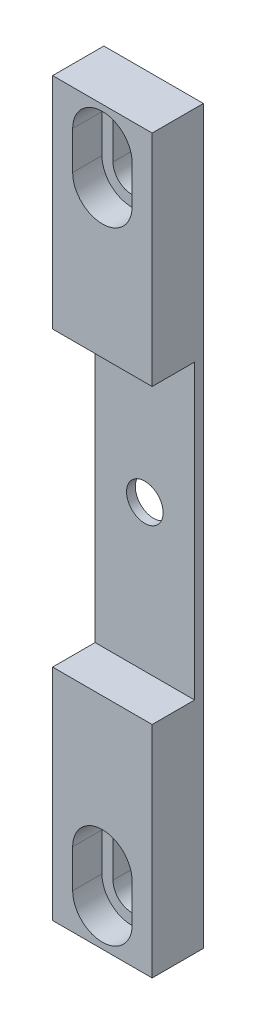
SolidWorks part; units mm, degrees
material "6061-T6 Al"
ref_plane "Front Plane" through (0, 0, 0) normal (0, 0, 1) x (1, 0, 0)
ref_plane "Top Plane" through (0, 0, 0) normal (0, 1, 0) x (1, 0, 0)
ref_plane "Right Plane" through (0, 0, 0) normal (1, 0, 0) x (0, 0, -1)
sketch "Sketch1" plane through (0, 0, 0) normal (0, 0, 1) x (1, 0, 0)
  line L0 (8.636, 63.5) -> (-8.636, -63.5) construction
  line L1 (-8.636, -63.5) -> (8.636, -63.5)
  line L2 (-8.636, -63.5) -> (-8.636, 63.5)
  line L3 (-8.636, 63.5) -> (8.636, 63.5)
  line L4 (8.636, -63.5) -> (8.636, 63.5)
  dimension "D2" = 127
  dimension "D4" = 17.272
extrude "Boss-Extrude1" add sketch "Sketch1" along normal blind 8.89
hole_wizard "1/4 (0.25) Diameter Hole1" positions "Sketch3" profile "Sketch4" hole size "1/4" standard "ANSI Inch" end condition up to next
sketch "Sketch3" plane through (0, 0, 8.89) normal (0, 0, 1) x (1, 0, 0)
  point P0 (0, 0)
sketch "Sketch4" plane through (0, 0, 8.89) normal (1, 0, 0) x (0, -1, 0)
  line L0 (0, 0) -> (0, 8.89)
  line L1 (0, 8.89) -> (3.175, 8.89)
  line L2 (3.175, 8.89) -> (3.175, 0)
  line L5 (3.175, 0) -> (0, 0)
  line L11 (0, -6.35) -> (0, 107.95) construction
  dimension "Thru Hole Dia." = 6.35
  dimension "Thru Hole Depth" = 8.89
sketch "Sketch5" plane through (0, 0, 8.89) normal (0, 0, 1) x (1, 0, 0)
  line L0 (-8.636, 63.5) -> (-8.636, -63.5) construction
  line L1 (-8.636, 25.4) -> (8.636, 25.4)
  line L2 (-8.636, 25.4) -> (-8.636, -25.4)
  line L3 (-8.636, -25.4) -> (8.636, -25.4)
  line L4 (8.636, 25.4) -> (8.636, -25.4)
  line L5 (8.636, -63.5) -> (8.636, 63.5) construction
  line L6 (-8.636, -63.5) -> (8.636, -63.5) construction
  dimension "D1" = 50.8
  dimension "D2" = 38.1
extrude "Cut-Extrude1" cut sketch "Sketch5" against normal blind 7.366
sketch "Sketch13" plane through (0, 0, 8.89) normal (0, 0, 1) x (1, 0, 0)
  line L0 (0, 0) -> (-17.272, 0) construction
  line L1 (8.636, 63.5) -> (-8.636, 63.5) construction
  line L2 (0, 57.277) -> (0, 50.673) construction
  line L3 (3.2385, 57.277) -> (3.2385, 50.673)
  line L4 (-3.2385, 57.277) -> (-3.2385, 50.673)
  line L5 (0, -57.277) -> (0, -50.673) construction
  line L6 (3.2385, -57.277) -> (3.2385, -50.673)
  line L7 (-3.2385, -57.277) -> (-3.2385, -50.673)
  arc A0 (3.2385, 57.277) -> (-3.2385, 57.277) centre (0, 57.277) ccw
  arc A1 (-3.2385, 50.673) -> (3.2385, 50.673) centre (0, 50.673) ccw
  arc A2 (3.2385, -57.277) -> (-3.2385, -57.277) centre (0, -57.277) cw
  arc A3 (-3.2385, -50.673) -> (3.2385, -50.673) centre (0, -50.673) cw
  point P7 (0, 53.975)
  point P14 (0, -53.975)
  dimension "D1" = 107.95
  dimension "D2" = 6.604
  dimension "D3" = 6.477
sketch "Sketch12" plane through (0, 0, 0) normal (0, 0, -1) x (-1, 0, 0)
  point P0 (0, 0)
extrude "Cut-Extrude2" cut sketch "Sketch13" against normal through all
sketch "Sketch14" plane through (0, 0, 8.89) normal (0, 0, 1) x (1, 0, 0)
  line L0 (0, 50.673) -> (0, 57.277) construction
  line L1 (-5.1594, 50.673) -> (-5.1594, 57.277)
  line L2 (5.1594, 50.673) -> (5.1594, 57.277)
  line L3 (0, -50.673) -> (0, -57.277) construction
  line L4 (5.1594, -50.673) -> (5.1594, -57.277)
  line L5 (-5.1594, -50.673) -> (-5.1594, -57.277)
  line L6 (3.2385, 57.277) -> (3.2385, 50.673) construction
  arc A0 (-5.1594, 50.673) -> (5.1594, 50.673) centre (0, 50.673) ccw
  arc A1 (5.1594, 57.277) -> (-5.1594, 57.277) centre (0, 57.277) ccw
  arc A2 (5.1594, -50.673) -> (-5.1594, -50.673) centre (0, -50.673) ccw
  arc A3 (-5.1594, -57.277) -> (5.1594, -57.277) centre (0, -57.277) ccw
  point P2 (0, 53.975)
  point P7 (0, -53.975)
  dimension "D1" = 10.3187
extrude "Cut-Extrude3" cut sketch "Sketch14" against normal blind 5.08
